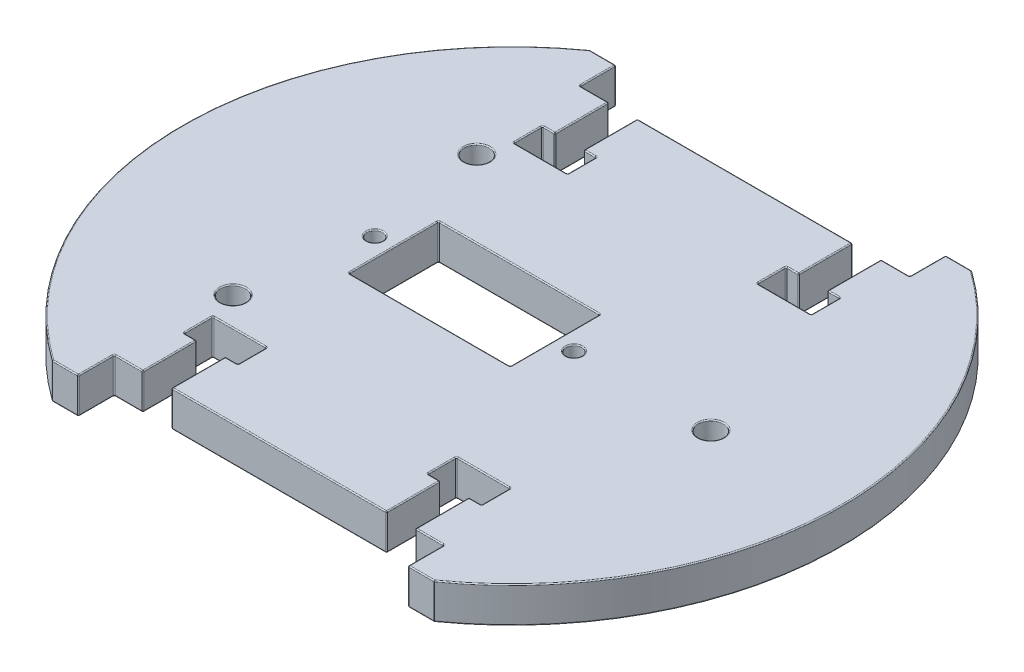
SolidWorks part; units mm, degrees
ref_plane "Płaszczyzna przednia" through (0, 0, 0) normal (0, 0, 1) x (1, 0, 0)
ref_plane "Płaszczyzna górna" through (0, 0, 0) normal (0, 1, 0) x (1, 0, 0)
ref_plane "Płaszczyzna prawa" through (0, 0, 0) normal (1, 0, 0) x (0, 0, -1)
sketch "Szkic1" plane through (0, 0, 0) normal (0, 1, 0) x (1, 0, 0)
  line L0 (-26.6411, 37.5) -> (-23, 37.5)
  line L1 (23, 37.5) -> (26.6411, 37.5)
  line L3 (-23, 37.5) -> (-23, 32.5)
  line L4 (-23, 32.5) -> (23, 32.5)
  line L5 (23, 37.5) -> (23, 32.5)
  line L6 (0, 0) -> (-46, 0) construction
  line L7 (23, -37.5) -> (26.6411, -37.5)
  line L8 (23, -37.5) -> (23, -32.5)
  line L9 (-23, -32.5) -> (23, -32.5)
  line L10 (-23, -37.5) -> (-23, -32.5)
  line L11 (-26.6411, -37.5) -> (-23, -37.5)
  line L12 (27.75, 0) -> (-21.93, 0) construction
  line L13 (-16.5, -6.25) -> (6, -6.25)
  line L14 (-16.5, -6.25) -> (-16.5, 6.25)
  line L15 (-16.5, 6.25) -> (6, 6.25)
  line L16 (6, -6.25) -> (6, 6.25)
  line L17 (-16.5, -6.25) -> (6, 6.25) construction
  line L18 (-16.5, 6.25) -> (6, -6.25) construction
  line L19 (-21.93, 17) -> (-21.93, -17) construction
  arc A0 (-26.6411, 37.5) -> (-26.6411, -37.5) centre (0, 0) ccw
  arc A1 (26.6411, -37.5) -> (26.6411, 37.5) centre (0, 0) ccw
  circle A2 centre (8.65, 0) radius 1.1
  circle A3 centre (-19.15, 0) radius 1.1
  circle A4 centre (27.75, 0) radius 1.75
  circle A5 centre (-21.93, 17) radius 1.75
  circle A6 centre (-21.93, -17) radius 1.75
  point P10 (0, 32.5)
  point P16 (-5.25, 0)
  point P25 (24.8206, 37.5)
  dimension "D1" = 92
  dimension "D7" = 2.2
  dimension "D8" = 2.2
  dimension "D15" = 3.5
  dimension "D2" = 22.5
  dimension "D3" = 46
  dimension "D4" = 5
  dimension "D5" = 12.5
  dimension "D6" = 6
  dimension "D9" = 2.65
  dimension "D10" = 2.65
  dimension "D11" = 37.5
  dimension "D12" = 34
  dimension "D13" = 27.75
  dimension "D14" = 49.68
extrude "Dodanie-wyciągnięcie1" add sketch "Szkic1" along normal blind 5
sketch "Szkic3" plane through (0, 5, 0) normal (0, 1, 0) x (1, 0, 0)
  line L0 (23, 32.5) -> (-23, 32.5) construction
  line L1 (-19, 25) -> (-15, 25)
  line L2 (-19, 25) -> (-19, 32.5)
  line L3 (-19, 32.5) -> (-15, 32.5)
  line L4 (-15, 25) -> (-15, 32.5)
  line L5 (-19, 25) -> (-15, 32.5) construction
  line L6 (-19, 32.5) -> (-15, 25) construction
  line L7 (-23, 32.5) -> (-23, 37.5) construction
  line L8 (-20.75, 21) -> (-13.25, 21)
  line L9 (-20.75, 21) -> (-20.75, 25)
  line L10 (-20.75, 25) -> (-13.25, 25)
  line L11 (-13.25, 21) -> (-13.25, 25)
  line L12 (-20.75, 21) -> (-13.25, 25) construction
  line L13 (-20.75, 25) -> (-13.25, 21) construction
  line L14 (-16.5, 0) -> (0, 0) construction
  line L15 (-16.5, 6.25) -> (-16.5, -6.25) construction
  line L16 (0, 0) -> (0, 32.5) construction
  line L17 (20.75, 25) -> (13.25, 21) construction
  line L18 (20.75, 21) -> (13.25, 25) construction
  line L19 (19, 32.5) -> (15, 25) construction
  line L20 (19, 25) -> (15, 32.5) construction
  line L21 (13.25, 21) -> (13.25, 25)
  line L22 (20.75, 25) -> (13.25, 25)
  line L23 (20.75, 21) -> (20.75, 25)
  line L24 (20.75, 21) -> (13.25, 21)
  line L25 (15, 25) -> (15, 32.5)
  line L26 (19, 32.5) -> (15, 32.5)
  line L27 (19, 25) -> (19, 32.5)
  line L28 (19, 25) -> (15, 25)
  line L29 (19, -25) -> (15, -32.5) construction
  line L30 (19, -32.5) -> (15, -25) construction
  line L31 (20.75, -21) -> (13.25, -25) construction
  line L32 (20.75, -25) -> (13.25, -21) construction
  line L33 (-20.75, -25) -> (-13.25, -21) construction
  line L34 (-20.75, -21) -> (-13.25, -25) construction
  line L35 (-19, -32.5) -> (-15, -25) construction
  line L36 (-19, -25) -> (-15, -32.5) construction
  line L37 (19, -25) -> (15, -25)
  line L38 (19, -25) -> (19, -32.5)
  line L39 (19, -32.5) -> (15, -32.5)
  line L40 (15, -25) -> (15, -32.5)
  line L41 (20.75, -21) -> (13.25, -21)
  line L42 (20.75, -21) -> (20.75, -25)
  line L43 (20.75, -25) -> (13.25, -25)
  line L44 (13.25, -21) -> (13.25, -25)
  line L45 (-13.25, -21) -> (-13.25, -25)
  line L46 (-20.75, -25) -> (-13.25, -25)
  line L47 (-20.75, -21) -> (-20.75, -25)
  line L48 (-20.75, -21) -> (-13.25, -21)
  line L49 (-15, -25) -> (-15, -32.5)
  line L50 (-19, -32.5) -> (-15, -32.5)
  line L51 (-19, -25) -> (-19, -32.5)
  line L52 (-19, -25) -> (-15, -25)
  point P0 (-17, 28.75)
  point P7 (-17, 23)
  point P28 (17, 23)
  point P29 (17, 28.75)
  point P46 (17, -28.75)
  point P47 (17, -23)
  point P48 (-17, -23)
  point P49 (-17, -28.75)
  dimension "D1" = 4
  dimension "D2" = 4
  dimension "D3" = 7.5
  dimension "D4" = 4
  dimension "D5" = 7.5
extrude "Wytnij-wyciągnięcie1" cut sketch "Szkic3" against normal through all contours L2 L1 L4 L3 | L9 L8 L11 L10 | L25 L26 L27 L28 | L21 L22 L23 L24 | L45 L46 L47 L48 | L49 L50 L51 L52 | L41 L44 L43 L42 | L37 L40 L39 L38
fillet "Zaokrąglenie1" radius 0.15 123 edges at (-15, 2.5, -25) (-19, 2.5, -32.5) (-19, 0, -28.75) (-19, 5, -28.75) (-15, 5, -28.75) (-13.25, 2.5, -21) (-20.75, 2.5, -21) (-20.75, 2.5, -25) (-20.75, 0, -23) (-17, 0, -21) (-19.875, 0, -25) (-14.125, 0, -25) (-20.75, 5, -23) (-17, 5, -21) (-13.25, 5, -23) (-14.125, 5, -25) (-13.25, 2.5, 21) (-13.25, 2.5, 25) (-20.75, 2.5, 21) (-19.875, 0, 25) (-14.125, 0, 25) (-13.25, 0, 23) (-17, 0, 21) (-19.875, 5, 25) (-14.125, 5, 25) (-13.25, 5, 23) (-17, 5, 21) (-15, 2.5, 32.5) (-19, 2.5, 32.5) (-19, 0, 28.75) (-15, 0, 28.75) (-19, 5, 28.75) (-15, 5, 28.75) (19, 2.5, 25) (20.75, 2.5, 25) (13.25, 2.5, 25) (20.75, 2.5, 21) (19.875, 0, 25) (20.75, 0, 23) (17, 5, 21) (13.25, 5, 23) (19.875, 5, 25) (14.125, 5, 25) (20.75, 5, 23) (15, 2.5, 32.5) (15, 0, 28.75) (19, 0, 28.75) (15, 5, 28.75) (19, 5, 28.75) (17, 5, -21) (14.125, 5, -25) (19.875, 5, -25) (20.75, 5, -23) (17, 0, -21) (13.25, 0, -23) (19.875, 0, -25) (20.75, 0, -23) (20.75, 2.5, -21) (20.75, 2.5, -25) (13.25, 2.5, -25) (13.25, 2.5, -21) (15, 5, -28.75) (15, 0, -28.75) (19, 0, -28.75) (19, 2.5, -25) (19, 2.5, -32.5) (15, 2.5, -32.5) (15, 2.5, -25) (-21.93, 0, 18.75) (-21.93, 5, 18.75) (-21.93, 0, -15.25) (-21.93, 5, -15.25) (27.75, 0, 1.75) (27.75, 5, 1.75) (-19.15, 5, 1.1) (8.65, 0, 1.1) (8.65, 5, 1.1) (-5.25, 0, -6.25) (-16.5, 0, 0) (-5.25, 0, 6.25) (6, 5, 0) (-5.25, 5, -6.25) (-16.5, 5, 0) (-5.25, 5, 6.25) (6, 2.5, 6.25) (-16.5, 2.5, 6.25) (-16.5, 2.5, -6.25) (23, 0, 35) (24.8206, 0, 37.5) (46, 0, 0) (24.8206, 0, -37.5) (-21, 0, -32.5) (0, 0, -32.5) (21, 0, -32.5) (-23, 0, -35) (-24.8206, 0, -37.5) (-24.8206, 0, 37.5) (-23, 0, 35) (21, 0, 32.5) (-21, 0, 32.5) (23, 5, 35) (24.8206, 5, 37.5) (46, 5, 0) (23, 5, -35) (-21, 5, -32.5) (0, 5, -32.5) (21, 5, -32.5) (-23, 5, -35) (-46, 5, 0) (-23, 5, 35) (21, 5, 32.5) (0, 5, 32.5) (-21, 5, 32.5) (23, 2.5, 32.5) (-23, 2.5, 37.5) (-26.6411, 2.5, 37.5) (-23, 2.5, -37.5) (-23, 2.5, -32.5) (23, 2.5, -32.5) (23, 2.5, -37.5) (26.6411, 2.5, -37.5) (26.6411, 2.5, 37.5) (-24.8206, 5, -37.5)
